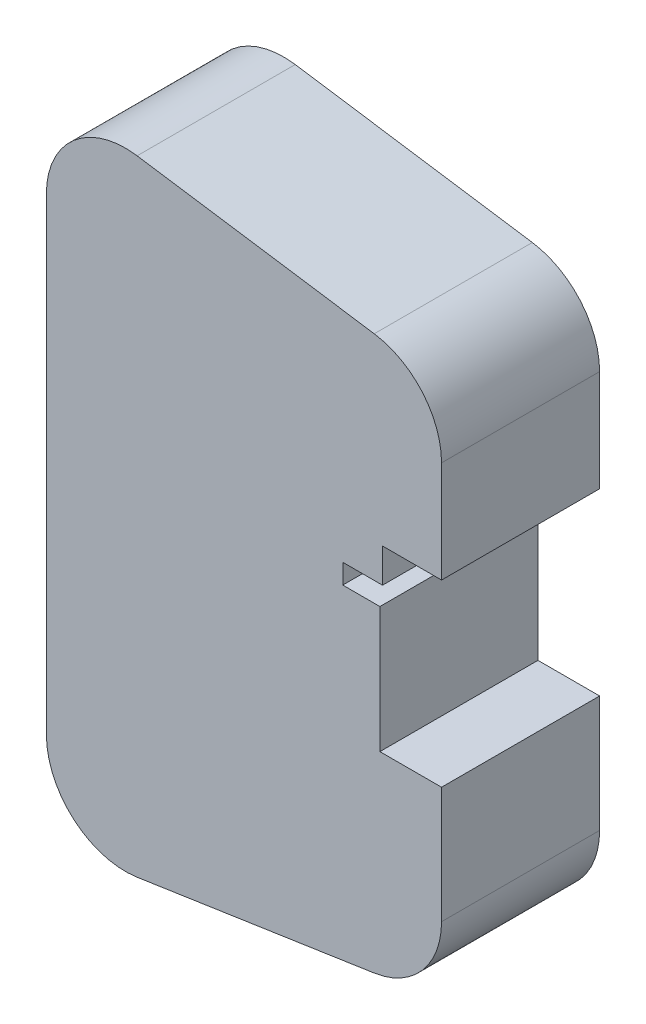
SolidWorks part; units mm, degrees
material "Polyurethane Foam Rigid"
ref_plane "Front Plane" through (0, 0, 0) normal (0, 0, 1) x (1, 0, 0)
ref_plane "Top Plane" through (0, 0, 0) normal (0, 1, 0) x (1, 0, 0)
ref_plane "Right Plane" through (0, 0, 0) normal (1, 0, 0) x (0, 0, -1)
sketch "Sketch1" plane through (0, 0, 0) normal (0, 0, 1) x (1, 0, 0)
  line L0 (0, 72.2334) -> (0, -72.2334) construction
  line L1 (0, 29.6381) -> (0, -29.6381)
  line L2 (-50, 0) -> (50, 0) construction
  line L3 (11.4834, 39.5275) -> (41.4834, 35.0275)
  line L4 (50, -25.1381) -> (50, 25.1381)
  line L5 (41.4834, -35.0275) -> (11.4834, -39.5275)
  arc A0 (41.4834, -35.0275) -> (50, -25.1381) centre (40, -25.1381) ccw
  arc A1 (41.4834, 35.0275) -> (50, 25.1381) centre (40, 25.1381) cw
  arc A2 (0, -29.6381) -> (11.4834, -39.5275) centre (10, -29.6381) ccw
  arc A3 (0, 29.6381) -> (11.4834, 39.5275) centre (10, 29.6381) cw
  point P13 (50, 0)
  point P14 (50, -33.75)
  point P17 (50, 33.75)
  point P20 (0, -41.25)
  point P23 (0, 41.25)
  point P24 (26.9612, 0)
  dimension "D4" = 10
  dimension "D5" = 10
  dimension "D1" = 50
  dimension "D2" = 82.5
  dimension "D3" = 67.5
extrude "Boss-Extrude1" add sketch "Sketch1" along normal blind 20
sketch "Sketch5" plane through (0, 0, 0) normal (-1, 0, 0) x (0, 0, 1)
  line L0 (10, 29.6381) -> (10, -29.6381) construction
  line L3 (20, 29.6381) -> (0, 29.6381) construction
  line L4 (20, -29.6381) -> (0, -29.6381) construction
  line L5 (5.5, 15.8428) -> (14.5, 15.8428)
  line L6 (5.5, 15.8428) -> (5.5, 17.2971)
  line L7 (5.5, 17.2971) -> (14.5, 17.2971)
  line L8 (14.5, 17.2971) -> (14.5, 15.8428)
  point P8 (10, 15.8428)
  point P9 (10, 17.2971)
  dimension "D1" = 9
extrude "Cut-Extrude4" cut sketch "Sketch5" against normal blind 10
sketch "Sketch6" plane through (0, 17.2971, 0) normal (0, -1, 0) x (1, 0, 0)
  line L0 (0, 10) -> (10.2544, 10) construction
  line L1 (0, 14.5) -> (0, 5.5) construction
  circle A0 centre (2.6449, 10) radius 0.5
extrude "Cut-Extrude5" cut sketch "Sketch6" against normal blind 5
sketch "Sketch9" plane through (0, 0, 20) normal (0, 0, 1) x (1, 0, 0)
  line L4 (50, -25.1381) -> (50, 25.1381) construction
  line L5 (42.2, 5.4971) -> (42.2, -10.4029)
  line L6 (42.53, 7.9971) -> (42.53, 12.2971)
  line L7 (42.53, 12.2971) -> (50, 12.2971)
  line L9 (42.2, -10.4029) -> (50, -10.4029)
  line L10 (37.5, 5.4971) -> (37.5, 7.9971)
  line L11 (42.2, 5.4971) -> (37.5, 5.4971)
  line L12 (37.5, 7.9971) -> (42.53, 7.9971)
  line L13 (50, 12.2971) -> (50, -10.4029)
  point P9 (42.2, -10.4029)
  point P10 (42.2, 5.4971)
  dimension "D2" = 7.8
  dimension "D3" = 4.7
extrude "Cut-Extrude6" cut sketch "Sketch9" against normal through all
sketch "Sketch11" plane through (0, 7.9971, 0) normal (0, -1, 0) x (-1, 0, 0)
  line L0 (-42.53, -10) -> (-37.5, -10) construction
  line L1 (-42.53, 0) -> (-42.53, -20) construction
  line L2 (-37.5, 0) -> (-37.5, -20) construction
  circle A0 centre (-40.23, -10) radius 1
  dimension "D1" = 2
  dimension "D2" = 2.3
extrude "Cut-Extrude7" cut sketch "Sketch11" against normal blind 5
